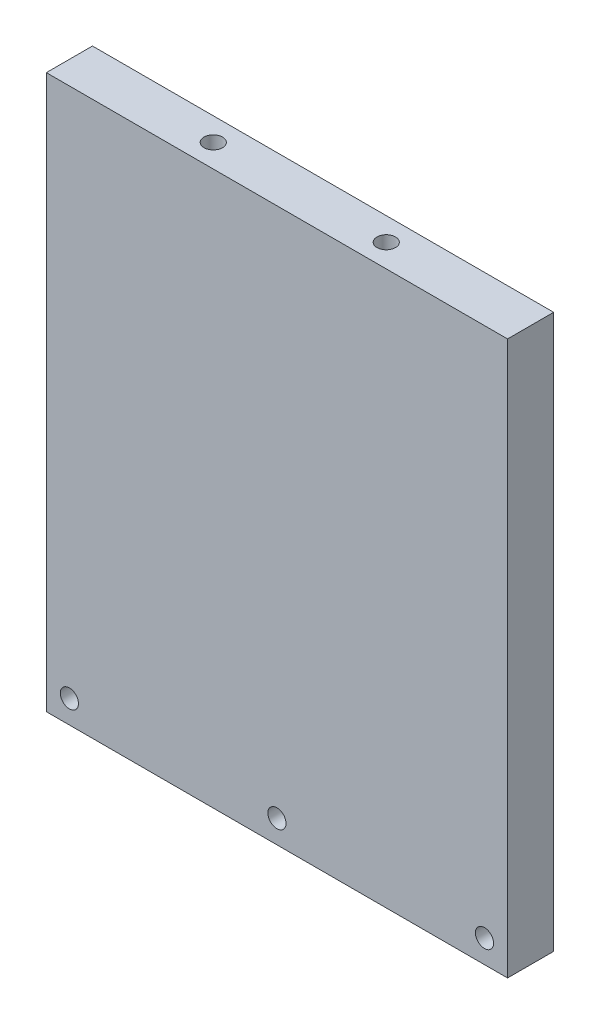
SolidWorks part; units mm, degrees
ref_plane "Front Plane" through (0, 0, 0) normal (0, 0, 1) x (1, 0, 0)
ref_plane "Top Plane" through (0, 0, 0) normal (0, 1, 0) x (1, 0, 0)
ref_plane "Right Plane" through (0, 0, 0) normal (1, 0, 0) x (0, 0, -1)
sketch "Sketch1" plane through (0, 0, 0) normal (0, 0, 1) x (1, 0, 0)
  line L0 (0, -152.4) -> (0, 152.4) construction
  line L1 (-127, -152.4) -> (127, -152.4)
  line L2 (-127, -152.4) -> (-127, 152.4)
  line L3 (-127, 152.4) -> (127, 152.4)
  line L4 (127, -152.4) -> (127, 152.4)
  line L5 (-127, -152.4) -> (127, 152.4) construction
  line L6 (-127, 152.4) -> (127, -152.4) construction
  line L7 (-127, -139.7) -> (127, -139.7) construction
  point P0 (0, 0)
  point P10 (0, -139.7)
  point P11 (-114.3, -139.7)
  point P12 (114.3, -139.7)
  dimension "D1" = 304.8
  dimension "D2" = 254
  dimension "D3" = 12.7
  dimension "D4" = 12.7
  dimension "D5" = 12.7
extrude "Boss-Extrude1" add sketch "Sketch1" along normal blind 25.4
hole_wizard "Ø10.0 (10) Diameter Hole1" positions "Sketch7" profile "Sketch8" hole size "Ø10.0" standard "ANSI Metric" end condition through all
sketch "Sketch7" plane through (0, 0, 25.4) normal (0, 0, 1) x (1, 0, 0)
  point P0 (-114.3, -139.7)
  point P3 (0, -139.7)
  point P6 (114.3, -139.7)
sketch "Sketch8" plane through (-114.3, -139.7, 25.4) normal (1, 0, 0) x (0, -1, 0)
  line L0 (0, 0) -> (0, 25.4)
  line L1 (0, 25.4) -> (5, 25.4)
  line L2 (5, 25.4) -> (5, 0)
  line L5 (5, 0) -> (0, 0)
  line L11 (0, -6.35) -> (0, 107.95) construction
  dimension "Thru Hole Dia." = 10
  dimension "Thru Hole Depth" = 25.4
sketch "Sketch9" plane through (0, 152.4, 0) normal (0, 1, 0) x (1, 0, 0)
  line L0 (-127, -12.7) -> (127, -12.7) construction
  line L1 (-127, -25.4) -> (-127, 0) construction
  line L2 (127, -25.4) -> (127, 0) construction
  line L3 (0, 0) -> (0, -25.4) construction
  line L4 (-127, 0) -> (127, 0) construction
  line L5 (127, -25.4) -> (-127, -25.4) construction
  point P12 (-47.754, -12.7)
  point P13 (47.498, -12.7)
  dimension "D1" = 47.754
  dimension "D2" = 47.498
hole_wizard "Tap Drill for M12x1.75 Tap1" positions "Sketch13" profile "Sketch12" hole size "M12x1.75" standard "ANSI Metric"
sketch "Sketch13" plane through (0, 152.4, 0) normal (0, 1, 0) x (1, 0, 0)
  point P0 (-47.754, -12.7)
  point P3 (47.498, -12.7)
sketch "Sketch12" plane through (-47.754, 152.4, 12.7) normal (1, 0, 0) x (0, 0, 1)
  line L0 (0, 0) -> (0, 33.0644)
  line L1 (0, 33.0644) -> (5.1, 30)
  line L2 (5.1, 30) -> (5.1, 0)
  line L5 (5.1, 0) -> (0, 0)
  line L10 (0, 33.0644) -> (-5.1, 30) construction
  line L11 (0, -6.35) -> (0, 107.95) construction
  dimension "Hole Dia." = 10.2
  dimension "Hole Depth" = 30
  dimension "Drill Angle" = 118
